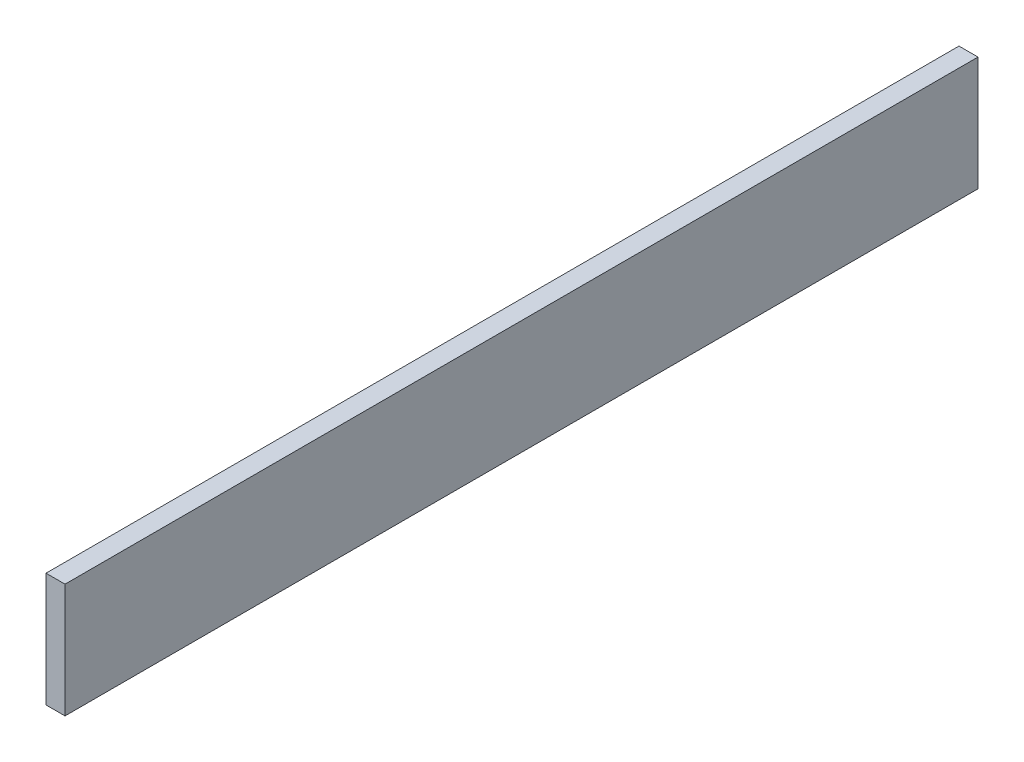
SolidWorks part; units mm, degrees
material "Acrylic (Medium-high impact)"
ref_plane "Front" through (0, 0, 0) normal (0, 0, 1) x (1, 0, 0)
ref_plane "Top" through (0, 0, 0) normal (0, 1, 0) x (1, 0, 0)
ref_plane "Right" through (0, 0, 0) normal (1, 0, 0) x (0, 0, -1)
sketch "Sketch1" plane through (0, 0, 0) normal (1, 0, 0) x (0, 0, -1)
  line L1 (-152.4, 38.1) -> (152.4, 38.1)
  line L2 (-152.4, 38.1) -> (-152.4, 0)
  line L3 (-152.4, 0) -> (152.4, 0)
  line L4 (152.4, 38.1) -> (152.4, 0)
  point P4 (0, 0)
  dimension "D1" = 304.8
  dimension "D2" = 38.1
extrude "Boss-Extrude1" add sketch "Sketch1" along normal blind 6.35
